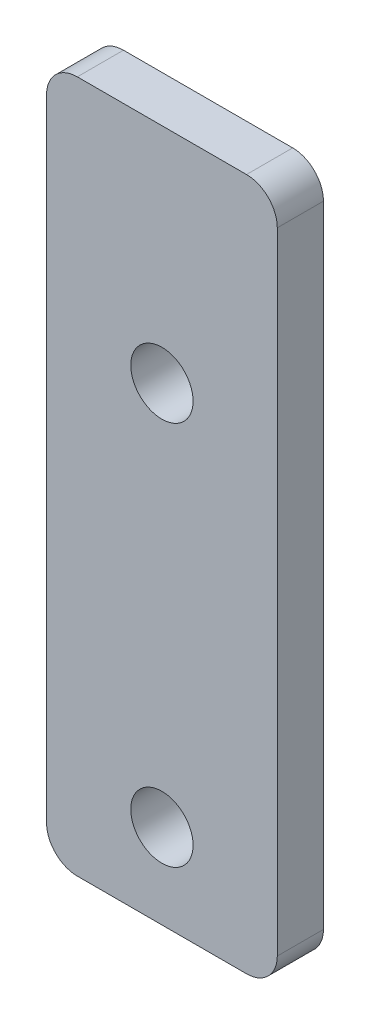
SolidWorks part; units mm, degrees
material "环氧玻璃布层压板"
ref_plane "前视基准面" through (0, 0, 0) normal (0, 0, 1) x (1, 0, 0)
ref_plane "上视基准面" through (0, 0, 0) normal (0, 1, 0) x (1, 0, 0)
ref_plane "右视基准面" through (0, 0, 0) normal (1, 0, 0) x (0, 0, -1)
sketch "草图1" plane through (0, 0, 0) normal (0, 0, 1) x (1, 0, 0)
  line L1 (-7.5, -22.5) -> (7.5, -22.5)
  line L2 (-7.5, -22.5) -> (-7.5, 22.5)
  line L3 (-7.5, 22.5) -> (7.5, 22.5)
  line L4 (7.5, -22.5) -> (7.5, 22.5)
  line L5 (0, 22.5) -> (0, -22.5) construction
  line L6 (-7.5, 0) -> (7.5, 0) construction
  point P0 (0, 0)
  dimension "D1" = 45
  dimension "D2" = 15
extrude "凸台-拉伸1" add sketch "草图1" along normal blind 3
sketch "草图2" plane through (0, 0, 3) normal (0, 0, 1) x (1, 0, 0)
  line L0 (0, -22.5) -> (0, -17) construction
  line L1 (-7.5, -22.5) -> (7.5, -22.5) construction
  line L2 (0, -17) -> (0, 8) construction
  circle A0 centre (0, -17) radius 2.025
  circle A1 centre (0, 8) radius 2.025
  dimension "D3" = 4.05
  dimension "D1" = 5.5
  dimension "D2" = 25
extrude "切除-拉伸1" cut sketch "草图2" against normal blind 3
fillet "圆角1" radius 2 4 edges at (7.5, -22.5, 1.5) (-7.5, -22.5, 1.5) (-7.5, 22.5, 1.5) (7.5, 22.5, 1.5)
